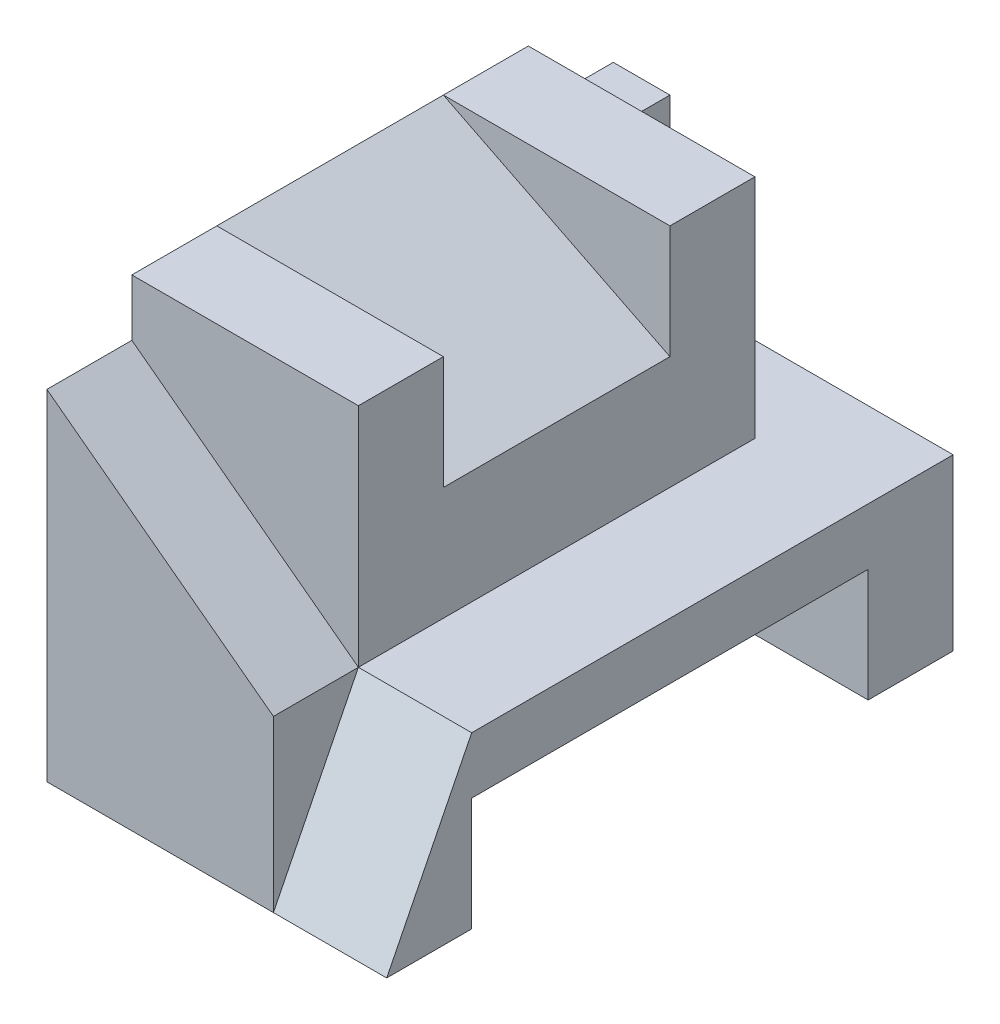
SolidWorks part; units mm, degrees
ref_plane "Alzado" through (0, 0, 0) normal (0, 0, 1) x (1, 0, 0)
ref_plane "Planta" through (0, 0, 0) normal (0, 1, 0) x (1, 0, 0)
ref_plane "Vista lateral" through (0, 0, 0) normal (1, 0, 0) x (0, 0, -1)
sketch "Croquis1" plane through (0, 0, 0) normal (0, 0, 1) x (1, 0, 0)
  line L0 (0, 0) -> (6, 0)
  line L1 (6, 0) -> (6, 3)
  line L2 (6, 3) -> (4, 3)
  line L3 (4, 3) -> (4, 7)
  line L4 (4, 7) -> (0, 7)
  line L5 (0, 7) -> (0, 0)
  dimension "D1" = 6
  dimension "D2" = 7
  dimension "D3" = 3
  dimension "D4" = 2
extrude "Saliente-Extruir1" add sketch "Croquis1" against normal blind 10
sketch "Croquis2" plane through (0, 0, 0) normal (0, 0, 1) x (1, 0, 0)
  line L0 (4, 3) -> (0, 6)
  line L1 (0, 7) -> (0, 0) construction
  line L2 (0, 6) -> (0, 7)
  line L3 (0, 7) -> (4, 7)
  line L4 (4, 7) -> (4, 3)
  dimension "D1" = 1
extrude "Cortar-Extruir1" cut sketch "Croquis2" against normal blind 1.5
sketch "Croquis4" plane through (6, 0, 0) normal (1, 0, 0) x (0, 0, -1)
  line L0 (1.5, 3) -> (0, 0)
  line L1 (10, 3) -> (0, 3) construction
  line L2 (10, 3) -> (1.5, 3) construction
  line L3 (0, 0) -> (0, 3)
  line L4 (0, 3) -> (1.5, 3)
  line L5 (1.5, 3) -> (1.5, 7) construction
  line L6 (1.5, 6) -> (1.5, 3) construction
  point P7 (1.5, 3)
extrude "Cortar-Extruir2" cut sketch "Croquis4" against normal blind 2
sketch "Croquis5" plane through (6, 0, 0) normal (1, 0, 0) x (0, 0, -1)
  line L0 (1.5, 0) -> (1.5, 2)
  line L1 (10, 0) -> (0, 0) construction
  line L2 (1.5, 2) -> (8.5, 2)
  line L3 (8.5, 2) -> (8.5, 0)
  line L4 (1.5, 0) -> (8.5, 0)
  line L6 (10, 0) -> (10, 3) construction
  dimension "D1" = 2
  dimension "D2" = 1.5
  dimension "D3" = 1.5
extrude "Cortar-Extruir3" cut sketch "Croquis5" against normal up to next
sketch "Croquis6" plane through (0, 0, -10) normal (0, 0, -1) x (-1, 0, 0)
  line L0 (-4, 7) -> (0, 7) construction
  line L1 (-4, 3) -> (-4, 7) construction
  line L2 (-4, 7) -> (0, 7)
  line L3 (-4, 3) -> (-4, 7)
  line L4 (-4, 3) -> (-1, 3)
  line L5 (-1, 3) -> (-1, 6)
  line L6 (-1, 6) -> (0, 6)
  line L7 (0, 7) -> (0, 0) construction
  line L8 (0, 6) -> (0, 7)
  point P3 (-3, 5.6322)
  dimension "D1" = 3
  dimension "D2" = 1
extrude "Cortar-Extruir4" cut sketch "Croquis6" against normal blind 1.5
ref_plane "Plano1" through (0, 0, -5) normal (0, 0, 1) x (1, 0, 0)
sketch "Croquis7" plane through (0, 0, -5) normal (0, 0, 1) x (1, 0, 0)
  line L0 (4, 3) -> (4, 7) construction
  line L1 (4, 7) -> (0, 7) construction
  line L2 (4, 5) -> (4, 7)
  line L3 (4, 7) -> (0, 7)
  line L4 (0, 7) -> (4, 5)
  point P2 (4, 4.8194)
  point P5 (4, 6.252)
  dimension "D1" = 2
extrude "Cortar-Extruir5" cut sketch "Croquis7" against normal mid plane 4
